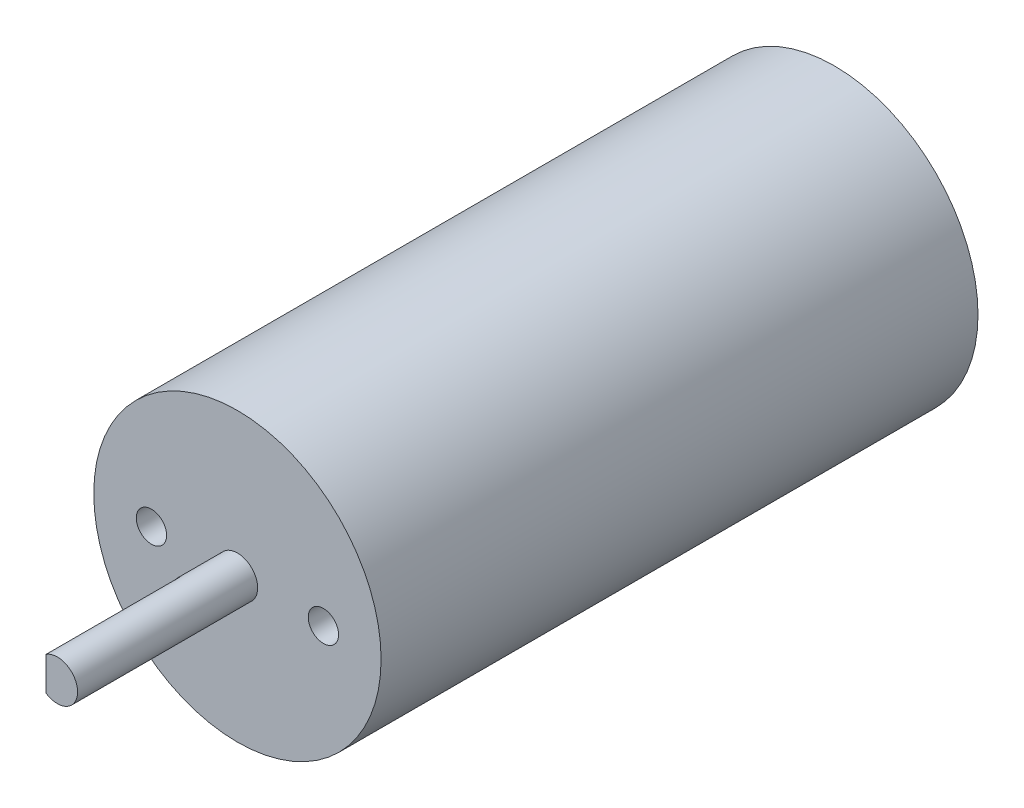
SolidWorks part; units mm, degrees
ref_plane "Front Plane" through (0, 0, 0) normal (0, 0, 1) x (1, 0, 0)
ref_plane "Top Plane" through (0, 0, 0) normal (0, 1, 0) x (1, 0, 0)
ref_plane "Right Plane" through (0, 0, 0) normal (1, 0, 0) x (0, 0, -1)
sketch "Sketch1" plane through (0, 0, 0) normal (0, 0, 1) x (1, 0, 0)
  circle A0 centre (0, 0) radius 14.2
  dimension "D1" = 28.4
extrude "Boss-Extrude1" add sketch "Sketch1" along normal blind 59
sketch "Sketch2" plane through (0, 0, 59) normal (0, 0, 1) x (1, 0, 0)
  circle A0 centre (0, 0) radius 2
  dimension "D1" = 4
extrude "Boss-Extrude2" add sketch "Sketch2" along normal blind 17.8
sketch "Sketch3" plane through (0, 0, 59) normal (0, 0, 1) x (1, 0, 0)
  line L0 (-14.2, 0) -> (14.2, 0) construction
  circle A0 centre (0, 0) radius 14.2 construction
  circle A1 centre (0, 0) radius 8.5 construction
  circle A2 centre (-8.5, 0) radius 1.5
  circle A3 centre (8.5, 0) radius 1.5
  dimension "D1" = 17
  dimension "D2" = 3
  dimension "D3" = 3
extrude "Cut-Extrude1" cut sketch "Sketch3" against normal blind 4.3942
ref_plane "Plane1" through (0, 0, 63.5) normal (0, 0, 1) x (1, 0, 0)
sketch "Sketch5" plane through (0, 0, 63.5) normal (0, 0, 1) x (1, 0, 0)
  line L1 (-1.1218, 2.0396) -> (-2.6515, 2.0396)
  line L2 (-1.1218, 2.0396) -> (-1.1218, -2.1416)
  line L3 (-1.1218, -2.1416) -> (-2.6515, -2.1416)
  line L4 (-2.6515, 2.0396) -> (-2.6515, -2.1416)
extrude "Cut-Extrude2" cut sketch "Sketch5" along normal blind 13.716
